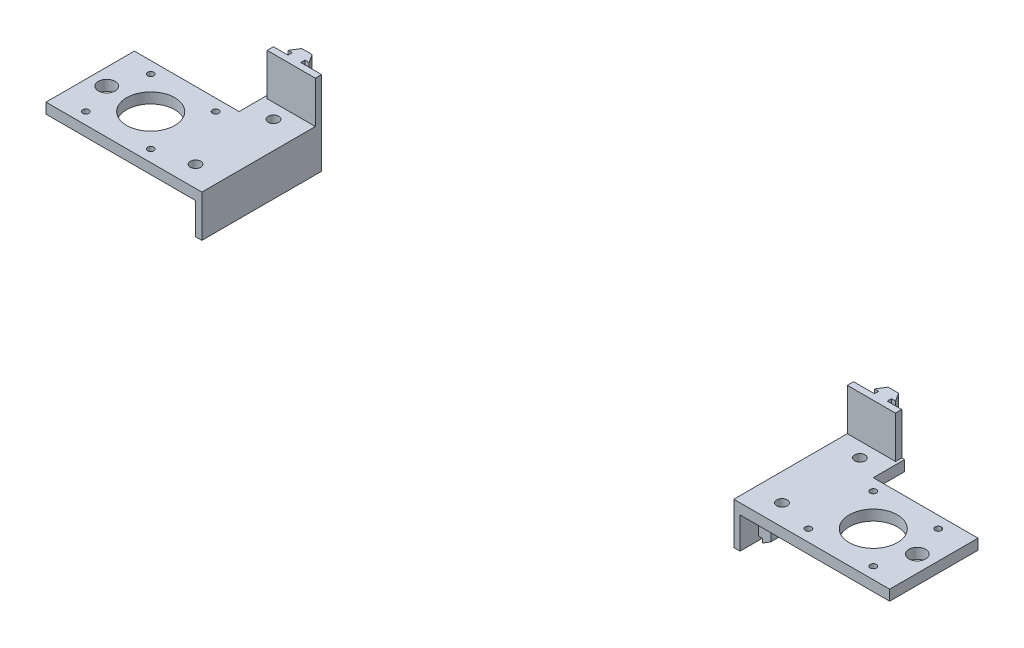
SolidWorks part; units mm, degrees
ref_plane "Front Plane" through (0, 0, 0) normal (0, 0, 1) x (1, 0, 0)
ref_plane "Top Plane" through (0, 0, 0) normal (0, 1, 0) x (1, 0, 0)
ref_plane "Right Plane" through (0, 0, 0) normal (1, 0, 0) x (0, 0, -1)
sketch "Sketch1" plane through (0, 0, 0) normal (0, 1, 0) x (1, 0, 0)
  line L0 (21.1, -21.1) -> (42.5, -21.1)
  line L1 (-21.1, -21.1) -> (21.1, -21.1)
  line L2 (-26.9, 13.1) -> (-26.9, 19.1)
  line L3 (-21.1, 21.1) -> (21.1, 21.1)
  line L4 (21.1, -21.1) -> (21.1, 21.1)
  line L5 (0, 21.1) -> (0, -21.1) construction
  line L6 (-21.1, 0) -> (21.1, 0) construction
  line L7 (42.5, -21.1) -> (42.5, 36.1)
  line L8 (42.5, 36.1) -> (21.1, 36.1)
  line L9 (21.1, 36.1) -> (21.1, 21.1)
  line L10 (22.5, -21.1) -> (22.5, 36.1) construction
  line L11 (-21.1, -21.1) -> (-28.9, -21.1)
  line L12 (-28.9, -21.1) -> (-28.9, 21.1)
  line L13 (-21.1, 21.1) -> (-28.9, 21.1)
  line L15 (-26.9, -13.1) -> (-26.9, -19.1)
  line L19 (-18.9, 13.1) -> (-18.9, 19.1)
  circle A0 centre (-15.5, 15.5) radius 1.5
  circle A1 centre (15.5, 15.5) radius 1.5
  circle A2 centre (15.5, -15.5) radius 1.5
  circle A3 centre (-15.5, -15.5) radius 1.5
  circle A4 centre (0, 0) radius 11.5
  circle A5 centre (32.5, 26.1) radius 2.5
  circle A6 centre (32.5, -11.1) radius 2.5
  circle A7 centre (-21, 0) radius 4
  point P0 (0, 0)
  dimension "D3" = 3
  dimension "D4" = 31
  dimension "D5" = 31
  dimension "D8" = 23
  dimension "D9" = 27
  dimension "D11" = 5
  dimension "D12" = 5
  dimension "D13" = 10
  dimension "D14" = 10
  dimension "D15" = 10
  dimension "D17" = 8
  dimension "D18" = 21
  dimension "D1" = 42.2
  dimension "D2" = 42.2
  dimension "D6" = 15.5
  dimension "D7" = 15.5
  dimension "D10" = 15
  dimension "D16" = 20
  dimension "D19" = 50
  dimension "D22" = 2
extrude "Boss-Extrude1" add sketch "Sketch1" along normal blind 5
sketch "Sketch2" plane through (42.5, 0, 0) normal (1, 0, 0) x (0, 0, -1)
  line L1 (-21.1, 5) -> (36.1, 5)
  line L2 (-21.1, 5) -> (-21.1, -18)
  line L3 (-21.1, -18) -> (36.1, -18)
  line L4 (36.1, 5) -> (36.1, -18)
  dimension "D1" = 23
extrude "Boss-Extrude2" add sketch "Sketch2" along normal blind 3
sketch "Sketch4" plane through (0, 0, -36.1) normal (0, 0, -1) x (-1, 0, 0)
  line L8 (-36.5, -7.5) -> (-40.5, -5)
  line L9 (-40.5, -5) -> (-40.5, -6.95)
  line L10 (-40.5, -6.95) -> (-42.5, -4.95)
  line L11 (-42.5, -4.95) -> (-42.5, -13.05)
  line L12 (-42.5, -13.05) -> (-40.5, -13.05)
  line L13 (-40.5, -13.05) -> (-40.5, -15)
  line L14 (-40.5, -15) -> (-36.5, -12.5)
  line L15 (-36.5, -12.5) -> (-36.5, -7.5)
  line L16 (-42.5, -18) -> (-42.5, 0) construction
  point P16 (-42.5, -9)
  point P19 (-42.5, -9)
  dimension "D1" = 2
extrude "Boss-Extrude3" add sketch "Sketch4" against normal blind 40 from offset 8.5 offset against normal yes
sketch "Sketch5" plane through (0, 0, 21.1) normal (0, 0, 1) x (1, 0, 0)
  line L1 (42.5, -15) -> (45.5, -15)
  line L2 (42.5, -15) -> (42.5, -18)
  line L3 (42.5, -18) -> (45.5, -18)
  line L4 (45.5, -15) -> (45.5, -18)
  dimension "D1" = 3
extrude "Cut-Extrude1" cut sketch "Sketch5" against normal through all
sketch "Sketch6" plane through (0, 0, -36.1) normal (0, 0, -1) x (-1, 0, 0)
  line L0 (-45.5, 5) -> (-21.1, 5) construction
  line L1 (-45.5, 5) -> (-22.5, 5)
  line L2 (-45.5, 5) -> (-45.5, 25)
  line L3 (-45.5, 25) -> (-22.5, 25)
  line L4 (-22.5, 5) -> (-22.5, 25)
  line L5 (-21.1, 5) -> (-21.1, 0) construction
  dimension "D1" = 23
  dimension "D2" = 20
  dimension "D3" = 1.4
extrude "Boss-Extrude4" add sketch "Sketch6" against normal blind 3
sketch "Sketch7" plane through (0, 25, 0) normal (0, 1, 0) x (1, 0, 0)
  line L0 (30, 42.1) -> (27.5, 38.1)
  line L1 (27.5, 38.1) -> (29.45, 38.1)
  line L2 (29.45, 38.1) -> (29.45, 36.1)
  line L3 (29.45, 36.1) -> (35.55, 36.1)
  line L4 (35.55, 36.1) -> (35.55, 38.1)
  line L5 (35.55, 38.1) -> (37.5, 38.1)
  line L6 (37.5, 38.1) -> (35, 42.1)
  line L7 (35, 42.1) -> (30, 42.1)
  line L9 (22.5, 36.1) -> (45.5, 36.1) construction
  line L10 (45.5, 36.1) -> (32.5, 36.1)
  point P13 (32.5, 36.1)
  line M3 (45.5, 36.1) -> (22.5, 36.1)
  dimension "D1" = 13
  dimension "D2" = 2
extrude "Boss-Extrude5" add sketch "Sketch7" against normal up to vertex contours L6 L7 L0 L1 L2 L3 L4 L5 M3
ref_plane "Plane1" through (172.5, 0, 0) normal (-1, 0, 0) x (0, 0, 1)
mirror "Mirror1" about plane through (172.5, 0, 0) normal (-1, 0, 0) of bodies 107
